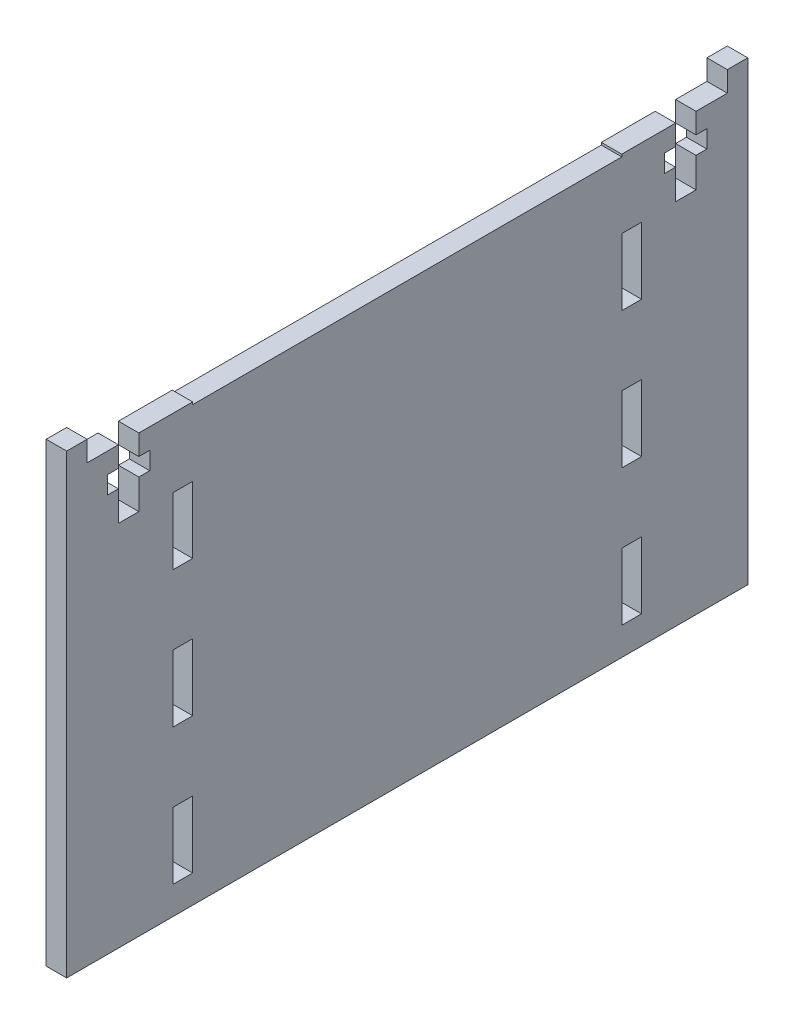
SolidWorks part; units mm, degrees
material "Acrylic (Medium-high impact)"
ref_plane "Front Plane" through (0, 0, 0) normal (0, 0, 1) x (1, 0, 0)
ref_plane "Top Plane" through (0, 0, 0) normal (0, 1, 0) x (1, 0, 0)
ref_plane "Right Plane" through (0, 0, 0) normal (1, 0, 0) x (0, 0, -1)
sketch "Sketch1" plane through (0, 0, 0) normal (1, 0, 0) x (0, 0, -1)
  line L1 (-31.5, -32) -> (31.5, -32) construction
  line L2 (-31.5, -32) -> (-31.5, 32) construction
  line L3 (-31.5, 32) -> (31.5, 32) construction
  line L4 (31.5, -32) -> (31.5, 32) construction
  line L5 (-31.5, -32) -> (31.5, 32) construction
  line L6 (-31.5, 32) -> (31.5, -32) construction
  line L7 (50, -32) -> (-50, -32)
  line L8 (50, -32) -> (50, 32)
  line L9 (50, 32) -> (-50, 32)
  line L10 (-50, -32) -> (-50, 32)
  line L11 (50, -32) -> (-50, 32) construction
  line L12 (50, 32) -> (-50, -32) construction
  point P0 (0, 0)
  point P6 (0, 0)
  dimension "D1" = 63
  dimension "D2" = 64
  dimension "D3" = 100
extrude "Boss-Extrude1" add sketch "Sketch1" along normal blind 3 contours L10 L9 L8 L7
sketch "Sketch2" plane through (3, 0, 0) normal (1, 0, 0) x (0, 0, -1)
  line L0 (31.5, -32) -> (31.5, 32) construction
  line L1 (-31.5, -32) -> (-31.5, 32) construction
  line L2 (31.5, -32) -> (31.5, 32) construction
  line L3 (-31.5, -32) -> (-31.5, 32) construction
  line L5 (-31.5, 21.9) -> (-34.4, 21.9)
  line L6 (-31.5, 21.9) -> (-31.5, 12.1)
  line L7 (-31.5, 12.1) -> (-34.4, 12.1)
  line L8 (-34.4, 21.9) -> (-34.4, 12.1)
  line L9 (50, 32) -> (-50, 32) construction
  line L10 (-31.5, 1.9) -> (-31.5, -7.9)
  line L11 (-31.5, 1.9) -> (-34.4, 1.9)
  line L12 (-34.4, 1.9) -> (-34.4, -7.9)
  line L13 (-31.5, -7.9) -> (-34.4, -7.9)
  line L14 (-31.5, -18.1) -> (-31.5, -27.9)
  line L15 (-31.5, -18.1) -> (-34.4, -18.1)
  line L16 (-34.4, -18.1) -> (-34.4, -27.9)
  line L17 (-31.5, -27.9) -> (-34.4, -27.9)
  line L18 (0, 0) -> (0, 32) construction
  line L19 (31.5, -18.1) -> (34.4, -18.1)
  line L20 (34.4, -18.1) -> (34.4, -27.9)
  line L21 (31.5, -27.9) -> (34.4, -27.9)
  line L22 (31.5, -18.1) -> (31.5, -27.9)
  line L23 (31.5, 1.9) -> (34.4, 1.9)
  line L24 (34.4, 1.9) -> (34.4, -7.9)
  line L25 (31.5, -7.9) -> (34.4, -7.9)
  line L26 (31.5, 1.9) -> (31.5, -7.9)
  line L27 (31.5, 12.1) -> (34.4, 12.1)
  line L28 (34.4, 21.9) -> (34.4, 12.1)
  line L29 (31.5, 21.9) -> (34.4, 21.9)
  line L30 (31.5, 21.9) -> (31.5, 12.1)
  dimension "D1" = 2.9
  dimension "D2" = 9.8
  dimension "D3" = 10.1
  dimension "D5" = 10.2
  dimension "D4" = 3
extrude "Cut-Extrude1" cut sketch "Sketch2" against normal blind 3
sketch "Sketch3" plane through (3, 0, 0) normal (1, 0, 0) x (0, 0, -1)
  line L0 (-31.75, 32) -> (31.75, 32) construction
  line L1 (0, 32) -> (0, 0) construction
  line L2 (50, 32) -> (-50, 32) construction
  line L3 (-42.4, 32) -> (-42.4, 29)
  line L4 (-42.4, 29) -> (-44, 29)
  line L5 (-44, 29) -> (-44, 26.4)
  line L6 (-44, 26.4) -> (-42.4, 26.4)
  line L7 (-42.4, 26.4) -> (-42.4, 22)
  line L8 (-42.4, 22) -> (-39.4, 22)
  line L9 (-42.4, 32) -> (-39.4, 32)
  line L10 (-40.9, 32) -> (-40.9, 22) construction
  line L11 (-39.4, 26.4) -> (-39.4, 22)
  line L12 (-37.8, 26.4) -> (-39.4, 26.4)
  line L13 (-37.8, 29) -> (-37.8, 26.4)
  line L14 (-39.4, 29) -> (-37.8, 29)
  line L15 (-39.4, 32) -> (-39.4, 29)
  line L16 (-34.4, 21.9) -> (-34.4, 12.1) construction
  dimension "D1" = 63.5
  dimension "D2" = 10
  dimension "D3" = 3
  dimension "D4" = 1.5
  dimension "D5" = 3.1
  dimension "D6" = 5
  dimension "D7" = 2.6
extrude "Cut-Extrude2" cut sketch "Sketch3" against normal blind 10
mirror "Mirror1" about plane through (0, 0, 0) normal (0, 0, 1) of "Cut-Extrude2"
sketch "Sketch5" plane through (3, 0, 0) normal (1, 0, 0) x (0, 0, -1)
  line L0 (39.4, 32) -> (-39.4, 32) construction
  line L1 (-31.5, 31.65) -> (31.5, 31.65)
  line L2 (-31.5, 31.65) -> (-31.5, 32)
  line L3 (-31.5, 32) -> (31.5, 32)
  line L4 (31.5, 31.65) -> (31.5, 32)
  line L5 (-31.5, 31.65) -> (31.5, 32) construction
  line L6 (-31.5, 32) -> (31.5, 31.65) construction
  line L7 (-31.5, 12.1) -> (-31.5, 21.9) construction
  line L9 (31.5, 21.9) -> (31.5, 12.1) construction
  point P0 (0, 31.825)
  dimension "D1" = 0.35
extrude "Cut-Extrude3" cut sketch "Sketch5" against normal blind 10
sketch "Sketch6" plane through (0, 0, 0) normal (-1, 0, 0) x (0, 0, 1)
  line L0 (0, 0) -> (0, 31.65) construction
  line L1 (-50, 32) -> (-47, 32)
  line L2 (-50, 32) -> (-50, 35)
  line L3 (-50, 35) -> (-47, 35)
  line L4 (-47, 32) -> (-47, 35)
  line L5 (-31.5, 31.65) -> (31.5, 31.65) construction
  line L6 (50, 35) -> (47, 35)
  line L7 (47, 32) -> (47, 35)
  line L8 (50, 32) -> (47, 32)
  line L9 (50, 32) -> (50, 35)
  dimension "D1" = 3
  dimension "D2" = 3
extrude "Boss-Extrude3" add sketch "Sketch6" against normal blind 3
